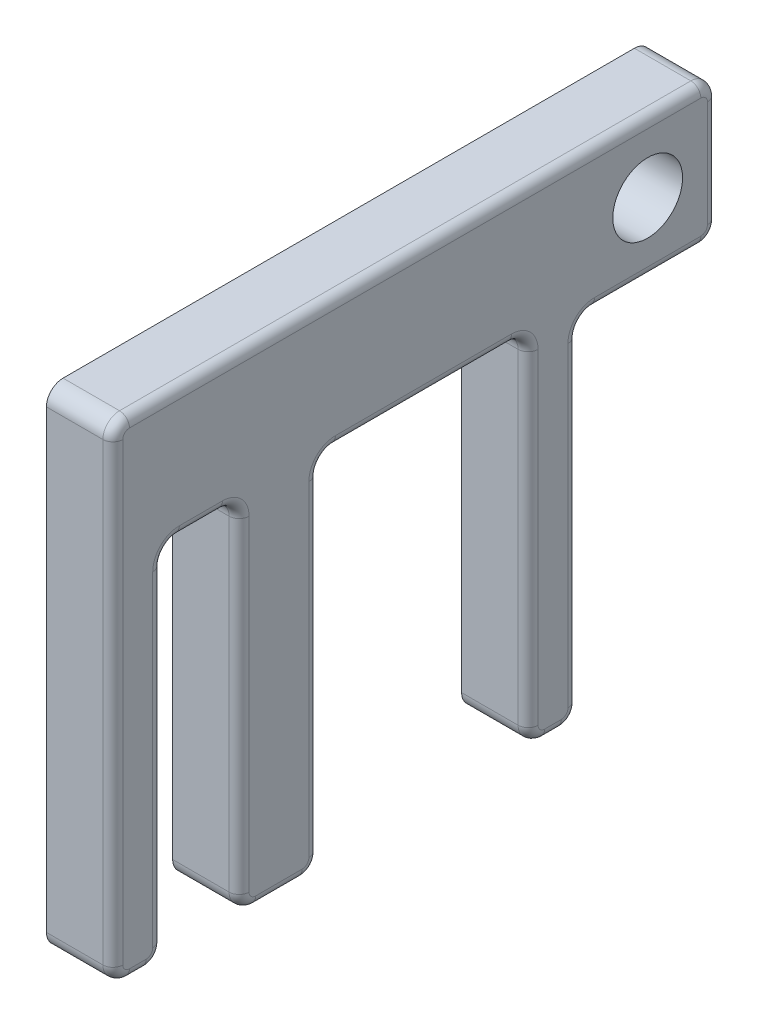
SolidWorks part; units mm, degrees
ref_plane "Front Plane" through (0, 0, 0) normal (0, 0, 1) x (1, 0, 0)
ref_plane "Top Plane" through (0, 0, 0) normal (0, 1, 0) x (1, 0, 0)
ref_plane "Right Plane" through (0, 0, 0) normal (1, 0, 0) x (0, 0, -1)
sketch "Sketch2" plane through (104.933, 0, 0) normal (1, 0, 0) x (0, 0, -1)
  line L0 (-107.3098, 81.5736) -> (-107.3098, 65.8256) construction
  line L1 (-107.3098, 65.8256) -> (-107.3098, 60.7456) construction
  line L2 (-107.3098, 60.7456) -> (-107.3098, 44.2356) construction
  line L3 (-107.3098, 44.2356) -> (-71.7498, 44.2356) construction
  line L4 (-71.7498, 70.9056) -> (-71.7498, 44.2356) construction
  line L5 (-71.7498, 70.9056) -> (-61.0818, 70.9056) construction
  line L6 (-61.0818, 70.9056) -> (-61.0818, 81.5736) construction
  line L7 (-107.3098, 81.5736) -> (-61.0818, 81.5736) construction
  line L8 (-107.3098, 81.5736) -> (-107.3098, 65.8256)
  line L9 (-107.3098, 65.8256) -> (-107.3098, 60.7456)
  line L10 (-107.3098, 60.7456) -> (-107.3098, 44.2356)
  line L11 (-107.3098, 44.2356) -> (-103.4998, 44.2356)
  line L12 (-71.7498, 70.9056) -> (-71.7498, 44.2356)
  line L13 (-71.7498, 70.9056) -> (-61.0818, 70.9056)
  line L14 (-61.0818, 70.9056) -> (-61.0818, 81.5736)
  line L15 (-107.3098, 81.5736) -> (-61.0818, 81.5736)
  line L16 (-73.2738, 78.0176) -> (-93.8478, 78.0176) construction
  line L17 (-73.2738, 46.7756) -> (-73.2738, 78.0176) construction
  line L18 (-93.8478, 78.0176) -> (-93.8478, 46.7756) construction
  line L19 (-93.8478, 46.7756) -> (-73.2738, 46.7756) construction
  line L20 (-105.7858, 46.7756) -> (-95.3718, 46.7756) construction
  line L21 (-95.3718, 46.7756) -> (-95.3718, 78.0176) construction
  line L22 (-105.7858, 78.0176) -> (-105.7858, 46.7756) construction
  line L23 (-95.3718, 78.0176) -> (-105.7858, 78.0176) construction
  line L24 (-73.2738, 78.0176) -> (-93.8478, 78.0176) construction
  line L25 (-73.2738, 46.7756) -> (-73.2738, 78.0176) construction
  line L26 (-93.8478, 78.0176) -> (-93.8478, 46.7756) construction
  line L27 (-93.8478, 46.7756) -> (-73.2738, 46.7756) construction
  line L28 (-105.7858, 46.7756) -> (-95.3718, 46.7756) construction
  line L29 (-95.3718, 46.7756) -> (-95.3718, 78.0176) construction
  line L30 (-105.7858, 78.0176) -> (-105.7858, 46.7756) construction
  line L31 (-95.3718, 78.0176) -> (-105.7858, 78.0176) construction
  line L32 (-103.4998, 71.6676) -> (-103.4998, 46.7756)
  line L33 (-97.6578, 46.7756) -> (-97.6578, 71.6676)
  line L34 (-91.5618, 71.6676) -> (-91.5618, 46.7756)
  line L35 (-75.5598, 46.7756) -> (-75.5598, 71.6676)
  line L36 (-97.6578, 71.6676) -> (-103.4998, 71.6676)
  line L37 (-75.5598, 71.6676) -> (-91.5618, 71.6676)
  line L38 (-95.3718, 71.6676) -> (-105.7858, 71.6676) construction
  line L39 (-103.4998, 78.0176) -> (-103.4998, 46.7756) construction
  line L40 (-97.6578, 46.7756) -> (-97.6578, 78.0176) construction
  line L41 (-73.2738, 71.6676) -> (-93.8478, 71.6676) construction
  line L42 (-91.5618, 78.0176) -> (-91.5618, 46.7756) construction
  line L43 (-75.5598, 46.7756) -> (-75.5598, 78.0176) construction
  line L44 (-103.4998, 46.7756) -> (-103.4998, 44.2356)
  line L45 (-97.6578, 46.7756) -> (-97.6578, 44.2356)
  line L46 (-91.5618, 46.7756) -> (-91.5618, 44.2356)
  line L47 (-75.5598, 46.7756) -> (-75.5598, 44.2356)
  line L48 (-75.5598, 44.2356) -> (-71.7498, 44.2356)
  line L49 (-97.6578, 44.2356) -> (-91.5618, 44.2356)
  circle A0 centre (-66.4158, 76.2396) radius 2.667 construction
  circle A1 centre (-66.4158, 76.2396) radius 2.667
  dimension "D1" = 2.286
  dimension "D2" = 6.35
extrude "Boss-Extrude1" add sketch "Sketch2" along normal blind 5.08
fillet "Fillet1" radius 1.27 14 edges at (107.473, 81.5736, 61.0818) (107.473, 70.9056, 61.0818) (107.473, 70.9056, 71.7498) (107.473, 71.6676, 91.5618) (107.473, 71.6676, 103.4998) (107.473, 71.6676, 97.6578) (107.473, 71.6676, 75.5598) (107.473, 44.2356, 71.7498) (107.473, 44.2356, 75.5598) (107.473, 44.2356, 91.5618) (107.473, 44.2356, 97.6578) (107.473, 44.2356, 103.4998) (107.473, 44.2356, 107.3098) (107.473, 81.5736, 107.3098)
fillet "Fillet2" radius 0.762 28 edges at (110.013, 70.5336, 71.3778) (110.013, 57.5706, 71.7498) (110.013, 44.6075, 72.1217) (110.013, 44.2356, 73.6548) (110.013, 44.6075, 75.1878) (110.013, 57.9516, 75.5598) (110.013, 71.2956, 75.9317) (110.013, 71.6676, 83.5608) (110.013, 71.2956, 91.1898) (110.013, 57.9516, 91.5618) (110.013, 44.6075, 91.9337) (110.013, 44.2356, 94.6098) (110.013, 44.6075, 97.2858) (110.013, 57.9516, 97.6578) (110.013, 71.2956, 98.0297) (110.013, 71.6676, 100.5788) (110.013, 71.2956, 103.1278) (110.013, 57.9516, 103.4998) (110.013, 44.6075, 103.8717) (110.013, 44.2356, 105.4048) (110.013, 44.6075, 106.9378) (110.013, 62.9046, 107.3098) (110.013, 81.2016, 106.9378) (110.013, 81.5736, 84.1958) (110.013, 81.2016, 61.4537) (110.013, 76.2396, 61.0818) (110.013, 71.2775, 61.4537) (110.013, 70.9056, 66.4158)
